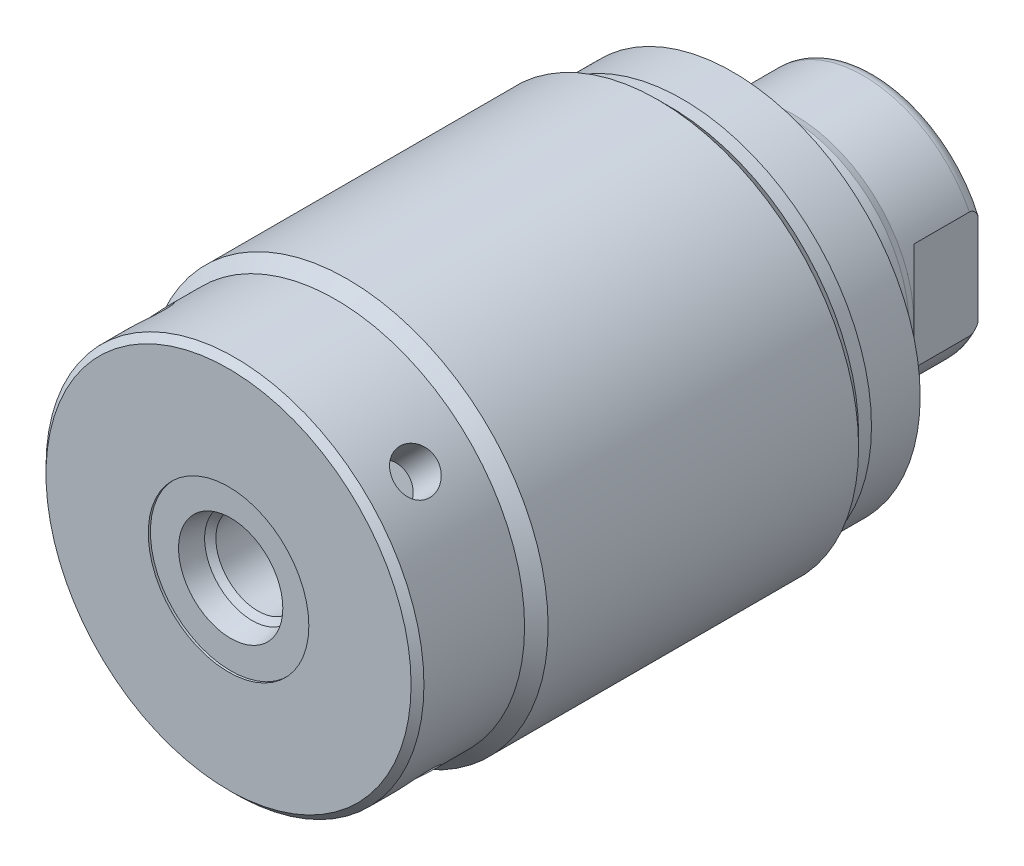
SolidWorks part; units mm, degrees
material "Alloy Steel"
ref_plane "Front Plane" through (0, 0, 0) normal (0, 0, 1) x (1, 0, 0)
ref_plane "Top Plane" through (0, 0, 0) normal (0, 1, 0) x (1, 0, 0)
ref_plane "Right Plane" through (0, 0, 0) normal (1, 0, 0) x (0, 0, -1)
ref_plane "Plane1" through (0, 0, 0) normal (0, 0, 1) x (1, 0, 0)
sketch "Sketch1" plane through (0, 0, 0) normal (0, 0, 1) x (1, 0, 0)
  circle A0 centre (0, 0) radius 23.8125
  dimension "D1" = 47.625
extrude "Extrude1" add sketch "Sketch1" along normal blind 53.848
sketch "Sketch2" plane through (0, 0, 0) normal (0, 1, 0) x (1, 0, 0)
  line L0 (23.8125, -53.848) -> (23.8125, -39.751)
  line L1 (23.8125, -39.751) -> (22.4155, -41.148)
  line L2 (22.4155, -41.148) -> (22.4155, -53.848)
  line L3 (22.4155, -53.848) -> (23.8125, -53.848)
  line L4 (0, 0) -> (0, -24.4965) construction
  line L5 (-23.8125, -53.848) -> (23.8125, -53.848) construction
  line L6 (23.8125, -53.848) -> (23.8125, 0) construction
  dimension "D1" = 12.7
  dimension "D2" = 44.831
  dimension "D3" = 45
revolve "Cut-Revolve1" cut sketch "Sketch2" angle 360 about L4
sketch "Sketch3" plane through (0, 0, 0) normal (0, 1, 0) x (1, 0, 0)
  line L0 (22.4155, 0) -> (22.4155, -1.524)
  line L1 (22.4155, -1.524) -> (23.8125, -2.921)
  line L2 (23.8125, -2.921) -> (23.8125, 0)
  line L3 (23.8125, 0) -> (22.4155, 0)
  line L4 (0, 0) -> (0, 3.0455) construction
  line L6 (23.8125, 0) -> (-23.8125, 0) construction
  line L7 (23.8125, -39.751) -> (23.8125, 0) construction
  dimension "D1" = 45
  dimension "D2" = 1.524
  dimension "D3" = 44.831
revolve "Cut-Revolve2" cut sketch "Sketch3" angle 360 about L4
sketch "S2D0002" plane through (0, 0, 0) normal (0, 1, 0) x (1, 0, 0)
  line L0 (6.1849, -53.594) -> (9.525, -53.594)
  line L1 (6.1849, -53.594) -> (5.6423, -51.0413)
  line L2 (5.6423, -51.0413) -> (4.9784, -50.3774)
  line L3 (4.9784, -50.3774) -> (4.9784, -39.624)
  line L4 (4.9784, -39.624) -> (0, -39.624)
  line L5 (0, -39.624) -> (0, -53.848)
  line L6 (0, -14.6685) -> (0, 0.6985) construction
  line L8 (9.525, -53.594) -> (9.525, -53.848)
  line L9 (-22.4155, -53.848) -> (22.4155, -53.848) construction
  line L10 (9.525, -53.848) -> (0, -53.848)
  dimension "D1" = 19.05
  dimension "D2" = 9.9568
  dimension "D3" = 0.254
  dimension "D4" = 12.3698
  dimension "D5" = 12
  dimension "D6" = 45
  dimension "D7" = 2.5527
  dimension "D8" = 13.97
revolve "Cut-Revolve3" cut sketch "S2D0002" angle 360 about L6
chamfer "Chamfer1" distance 0.762 angle 45 1 edges at (-22.4155, 0, 53.848)
sketch "Sketch6" plane through (0, 0, 0) normal (0, 0, -1) x (-1, 0, 0)
  circle A0 centre (0, 0) radius 22.225
  circle A1 centre (0, 0) radius 23.8125 construction
  dimension "D1" = 44.45
extrude "Extrude2" add sketch "Sketch6" along normal blind 5.969
sketch "Sketch7" plane through (0, 0, 0) normal (1, 0, 0) x (0, 0, -1)
  line L0 (5.969, 0) -> (5.969, -14.2875)
  line L1 (5.969, -14.2875) -> (22.479, -14.2875)
  line L2 (22.479, -14.2875) -> (22.479, 0)
  line L3 (22.479, 0) -> (5.969, 0)
  line L4 (0, 0) -> (9.7123, 0) construction
  line L5 (5.969, -22.225) -> (5.969, 22.225) construction
  dimension "D1" = 28.575
  dimension "D2" = 16.51
revolve "Revolve1" add sketch "Sketch7" angle 360 about L4
sketch "S2D0001" plane through (0, 0, 0) normal (0, 1, 0) x (1, 0, 0)
  line L0 (5.5499, 20.4113) -> (5.5499, 3.8608)
  line L1 (5.5499, 3.8608) -> (0, 3.8608)
  line L2 (6.7437, 22.479) -> (0, 22.479)
  line L3 (0, 22.479) -> (0, 3.8608)
  line L4 (5.5499, 20.4113) -> (6.7437, 22.479)
  line L5 (0, -31.3084) -> (0, 2.765) construction
  line L6 (14.2875, 22.479) -> (-14.2875, 22.479) construction
  dimension "D1" = 13.4874
  dimension "D2" = 30
  dimension "D3" = 18.6182
  dimension "D4" = 11.0998
revolve "Cut-Revolve5" cut sketch "S2D0001" angle 360 about L5
ref_plane "Plane8" through (0, 0, 0) normal (1, 0, 0) x (0, -1, 0)
sketch "Sketch9" plane through (0, 0, 0) normal (1, 0, 0) x (0, -1, 0)
  line L0 (-14.2875, 12.573) -> (-14.097, 13.335)
  line L1 (-14.097, 13.335) -> (-14.097, 21.463)
  line L2 (0, 12.6594) -> (0, 20.8178) construction
  line L3 (14.2875, 22.479) -> (-14.2875, 22.479) construction
  line L4 (-13.7089, 22.479) -> (-14.2875, 22.479)
  line L5 (-14.2875, 22.479) -> (-14.2875, 12.573)
  arc A0 (-13.7089, 22.479) -> (-14.097, 21.463) centre (-12.573, 21.463) ccw
  dimension "D1" = 1.524
  dimension "D2" = 1.016
  dimension "D3" = 28.194
  dimension "D4" = 0.762
  dimension "D5" = 9.144
revolve "Cut-Revolve6" cut sketch "Sketch9" angle 360 about L2
sketch "Sketch13" plane through (0, 0, 0) normal (0, 1, 0) x (1, 0, 0)
  line L0 (12.573, 22.479) -> (12.573, 14.9098)
  line L1 (12.573, 14.9098) -> (14.2875, 13.1953)
  line L2 (-12.573, 22.479) -> (-12.573, 14.9098)
  line L3 (-12.573, 14.9098) -> (-14.2875, 13.1953)
  line L4 (13.7089, 22.479) -> (-13.7089, 22.479) construction
  line L5 (0, 13.7262) -> (0, 20.767) construction
  line L6 (14.2875, 13.1953) -> (14.2875, 22.479)
  line L8 (12.573, 22.479) -> (14.2875, 22.479)
  line L10 (-14.2875, 13.1953) -> (-14.2875, 22.479)
  line L11 (-12.573, 22.479) -> (-14.2875, 22.479)
  line L12 (14.2875, 5.969) -> (14.2875, 12.573) construction
  dimension "D1" = 25.146
  dimension "D2" = 135
  dimension "D3" = 7.5692
extrude "Cut-Extrude4" cut sketch "Sketch13" against normal mid plane 39.685
ref_plane "Plane13" through (0, 0, 0) normal (0.7071, 0.7071, 0) x (0, 0, -1)
hole_wizard "Hole1" positions "3DSketch2" profile "Sketch14" legacy
sketch3d "3DSketch2"
  point P0 (-15.8502, 15.8502, 47.498)
  dimension "D1" = 6.35
sketch "Sketch14" plane through (-15.8502, 15.8502, 47.498) normal (0, 0, 1) x (-0.7071, -0.7071, 0)
  line L0 (0, 0) -> (0, 4.7498)
  line L1 (0, 4.7498) -> (2.5019, 4.7498)
  line L2 (2.5019, 4.7498) -> (2.5019, 0)
  line L3 (2.5019, 0) -> (0, 0)
  line L4 (0, 110) -> (0, -10) construction
  dimension "Diameter" = 5.0038
  dimension "Depth" = 4.7498
pattern_circular "CirPattern1" count 4 over 360 about axis through (0, 0, 0) along (0, 0, 1) of "Hole1"
